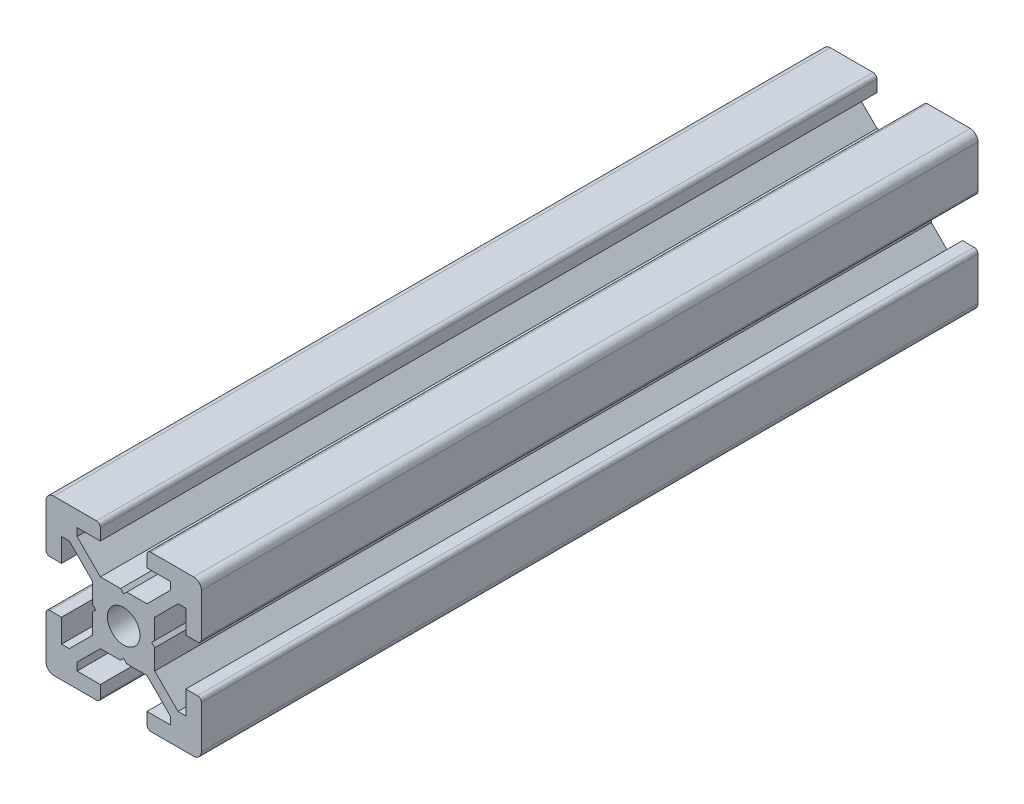
SolidWorks part; units mm, degrees
material "Lega 6061"
ref_plane "Piano frontale" through (0, 0, 0) normal (0, 0, 1) x (1, 0, 0)
ref_plane "Piano superiore" through (0, 0, 0) normal (0, 1, 0) x (1, 0, 0)
ref_plane "Piano destro" through (0, 0, 0) normal (1, 0, 0) x (0, 0, -1)
sketch "Schizzo1" plane through (0, 0, 0) normal (0, 0, 1) x (1, 0, 0)
  line L0 (0, 0) -> (-10, 0) construction
  line L1 (0, 0) -> (0, 10) construction
  line L2 (-3.6, 0) -> (-4, 0.4)
  line L3 (-4, 0.4) -> (-4, 3)
  line L4 (-4, 3) -> (-7, 6)
  line L5 (-7, 6) -> (-8, 6)
  line L6 (-8, 6) -> (-8, 3)
  line L7 (-8, 3) -> (-9.5, 3)
  line L8 (-10, 3.5) -> (-10, 9)
  line L9 (0, 0) -> (-10, 10) construction
  line L10 (0, 3.6) -> (-0.4, 4)
  line L11 (-0.4, 4) -> (-3, 4)
  line L12 (-3, 4) -> (-6, 7)
  line L13 (-6, 7) -> (-6, 8)
  line L14 (-6, 8) -> (-3, 8)
  line L15 (-3, 8) -> (-3, 9.5)
  line L16 (-3.5, 10) -> (-9, 10)
  line L17 (0, 0) -> (-10, -10) construction
  line L18 (-3.5, -10) -> (-9, -10)
  line L19 (-3, -8) -> (-3, -9.5)
  line L20 (-6, -8) -> (-3, -8)
  line L21 (-6, -7) -> (-6, -8)
  line L22 (-3, -4) -> (-6, -7)
  line L23 (-0.4, -4) -> (-3, -4)
  line L24 (0, -3.6) -> (-0.4, -4)
  line L25 (-10, -3.5) -> (-10, -9)
  line L26 (-8, -3) -> (-9.5, -3)
  line L27 (-8, -6) -> (-8, -3)
  line L28 (-7, -6) -> (-8, -6)
  line L29 (-4, -3) -> (-7, -6)
  line L30 (-4, -0.4) -> (-4, -3)
  line L31 (-3.6, 0) -> (-4, -0.4)
  line L32 (0, 0) -> (10, -10) construction
  line L33 (0, 0) -> (10, 10) construction
  line L34 (3.6, 0) -> (4, -0.4)
  line L35 (4, -0.4) -> (4, -3)
  line L36 (4, -3) -> (7, -6)
  line L37 (7, -6) -> (8, -6)
  line L38 (8, -6) -> (8, -3)
  line L39 (8, -3) -> (9.5, -3)
  line L40 (10, -3.5) -> (10, -9)
  line L41 (0, -3.6) -> (0.4, -4)
  line L42 (0.4, -4) -> (3, -4)
  line L43 (3, -4) -> (6, -7)
  line L44 (6, -7) -> (6, -8)
  line L45 (6, -8) -> (3, -8)
  line L46 (3, -8) -> (3, -9.5)
  line L47 (3.5, -10) -> (9, -10)
  line L48 (3.5, 10) -> (9, 10)
  line L49 (3, 8) -> (3, 9.5)
  line L50 (6, 8) -> (3, 8)
  line L51 (6, 7) -> (6, 8)
  line L52 (3, 4) -> (6, 7)
  line L53 (0.4, 4) -> (3, 4)
  line L54 (0, 3.6) -> (0.4, 4)
  line L55 (10, 3.5) -> (10, 9)
  line L56 (8, 3) -> (9.5, 3)
  line L57 (8, 6) -> (8, 3)
  line L58 (7, 6) -> (8, 6)
  line L59 (4, 3) -> (7, 6)
  line L60 (4, 0.4) -> (4, 3)
  line L61 (3.6, 0) -> (4, 0.4)
  arc A0 (-10, 9) -> (-9, 10) centre (-9, 9) cw
  arc A1 (-3, 9.5) -> (-3.5, 10) centre (-3.5, 9.5) ccw
  arc A2 (-9.5, 3) -> (-10, 3.5) centre (-9.5, 3.5) cw
  arc A3 (-9.5, -3) -> (-10, -3.5) centre (-9.5, -3.5) ccw
  arc A4 (-3, -9.5) -> (-3.5, -10) centre (-3.5, -9.5) cw
  arc A5 (-10, -9) -> (-9, -10) centre (-9, -9) ccw
  arc A6 (10, -9) -> (9, -10) centre (9, -9) cw
  arc A7 (3, -9.5) -> (3.5, -10) centre (3.5, -9.5) ccw
  arc A8 (9.5, -3) -> (10, -3.5) centre (9.5, -3.5) cw
  arc A9 (9.5, 3) -> (10, 3.5) centre (9.5, 3.5) ccw
  arc A10 (3, 9.5) -> (3.5, 10) centre (3.5, 9.5) cw
  arc A11 (10, 9) -> (9, 10) centre (9, 9) ccw
  circle A12 centre (0, 0) radius 2.1
  point P24 (-3, 10)
  point P27 (-10, 3)
  point P49 (-10, -3)
  point P50 (-3, -10)
  point P92 (3, -10)
  point P93 (10, -3)
  point P94 (10, 3)
  point P95 (3, 10)
  dimension "D2" = 1
  dimension "D12" = 0.5
  dimension "D13" = 4.2
  dimension "D3" = 8
  dimension "D4" = 0.4
  dimension "D5" = 45
  dimension "D6" = 6
  dimension "D7" = 12
  dimension "D8" = 20
  dimension "D9" = 2
  dimension "D10" = 4
  dimension "D11" = 45
extrude "Estrusione-Estrusione1" add sketch "Schizzo1" along normal blind 100
